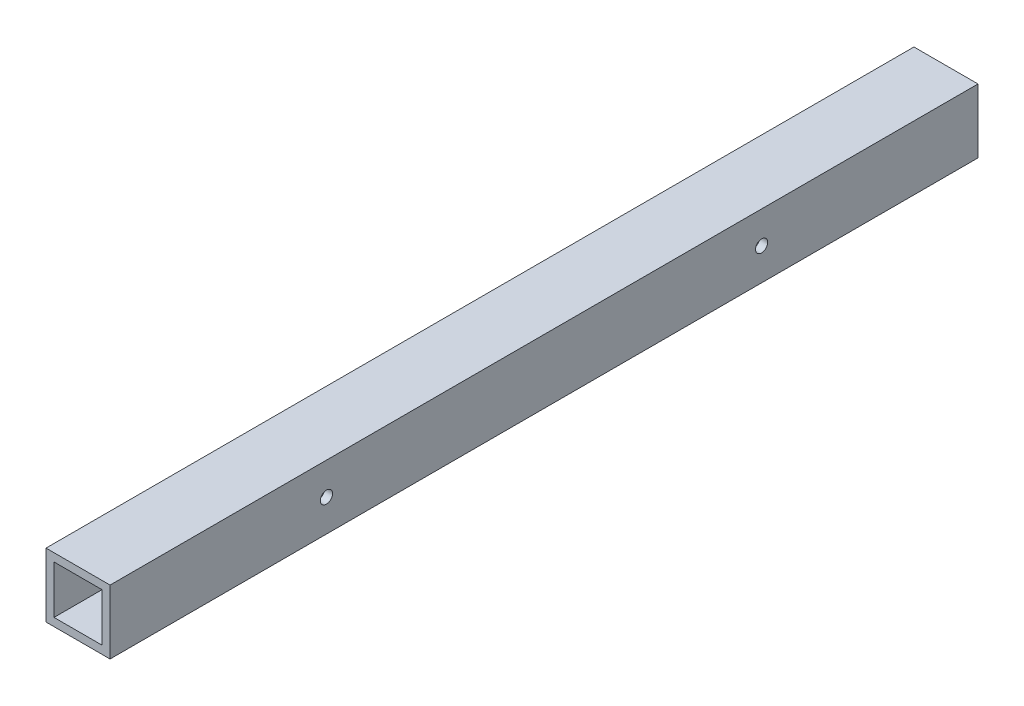
SolidWorks part; units mm, degrees
material "6061-T6 (SS)"
ref_plane "Front" through (0, 0, 0) normal (0, 0, 1) x (1, 0, 0)
ref_plane "Top" through (0, 0, 0) normal (0, 1, 0) x (1, 0, 0)
ref_plane "Right" through (0, 0, 0) normal (1, 0, 0) x (0, 0, -1)
sketch "Sketch1" plane through (0, 0, 0) normal (0, 0, 1) x (1, 0, 0)
  line L1 (0, 0) -> (25.4, 0)
  line L2 (0, 0) -> (0, 25.4)
  line L3 (0, 25.4) -> (25.4, 25.4)
  line L4 (25.4, 0) -> (25.4, 25.4)
  dimension "D1" = 25.4
extrude "Extrude-Thin1" add sketch "Sketch1" along normal blind 344.17 thin thin type one direction reverse wall 3.175
ref_plane "Plane1" through (0, 0, 172.085) normal (0, 0, 1) x (1, 0, 0)
sketch "Sketch2" plane through (25.4, 0, 0) normal (1, 0, 0) x (0, 0, -1)
  circle A0 centre (-85.8071, 12.7) radius 2.413 construction
  circle A1 centre (-258.3629, 12.7) radius 2.413 construction
  circle A2 centre (-85.8071, 12.7) radius 2.413
  circle A3 centre (-258.3629, 12.7) radius 2.413
extrude "Cut-Extrude1" cut sketch "Sketch2" against normal through all
